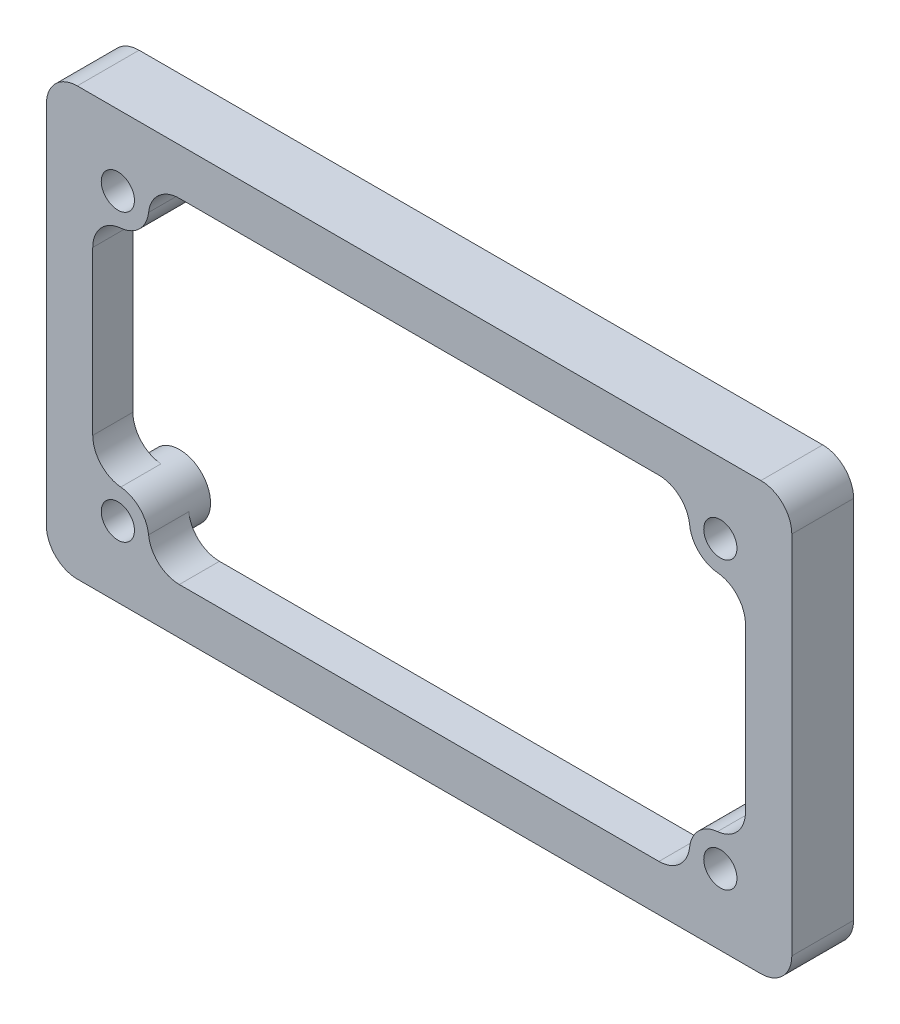
SolidWorks part; units mm, degrees
material "ABS"
ref_plane "Front Plane" through (0, 0, 0) normal (0, 0, 1) x (1, 0, 0)
ref_plane "Top Plane" through (0, 0, 0) normal (0, 1, 0) x (1, 0, 0)
ref_plane "Right Plane" through (0, 0, 0) normal (1, 0, 0) x (0, 0, -1)
sketch "Sketch1" plane through (0, 0, 0) normal (0, 0, 1) x (1, 0, 0)
  line L0 (-1.5, 26.15) -> (46.75, 26.15)
  line L1 (0, 0) -> (45.25, 0)
  line L2 (0, 0) -> (0, 24.65)
  line L3 (0, 24.65) -> (45.25, 24.65)
  line L4 (45.25, 0) -> (45.25, 24.65)
  line L5 (46.75, -1.5) -> (46.75, 26.15)
  line L6 (-1.5, -1.5) -> (46.75, -1.5)
  line L7 (-1.5, -1.5) -> (-1.5, 26.15)
  dimension "D1" = 24.65
  dimension "D2" = 45.25
  dimension "D3" = 1.5
extrude "Main Body" add sketch "Sketch1" along normal blind 4
sketch "Sketch3" plane through (0, 0, 4) normal (0, 0, 1) x (1, 0, 0)
  line L0 (0, 24.65) -> (0, 0)
  line L1 (0, 0) -> (45.25, 0)
  line L2 (45.25, 0) -> (45.25, 24.65)
  line L3 (45.25, 24.65) -> (0, 24.65)
  line L4 (1.5, 23.15) -> (1.5, 1.5)
  line L5 (1.5, 1.5) -> (43.75, 1.5)
  line L6 (43.75, 1.5) -> (43.75, 23.15)
  line L7 (43.75, 23.15) -> (1.5, 23.15)
  dimension "D1" = 1.5
extrude "Boss-Extrude2" add sketch "Sketch3" against normal offset from surface (2.6 mm away) 1.4 up to face at (22.625, 12.325, 0)
sketch "Sketch4" plane through (0, 0, 1.4) normal (0, 0, -1) x (-1, 0, 0)
  line L0 (0, 12.325) -> (-45.25, 12.325) construction
  line L1 (0, 24.65) -> (0, 0) construction
  line L2 (-45.25, 0) -> (-45.25, 24.65) construction
  line L3 (-22.625, 12.325) -> (-22.625, 24.65) construction
  line L4 (-45.25, 24.65) -> (0, 24.65) construction
  line L5 (-1.125, 21.575) -> (-1.125, 23.575)
  line L6 (-1.125, 23.575) -> (-3.125, 23.575)
  line L7 (-1.125, 1.075) -> (-3.125, 1.075)
  line L8 (-1.125, 3.075) -> (-1.125, 1.075)
  line L9 (-44.125, 3.075) -> (-44.125, 1.075)
  line L10 (-44.125, 1.075) -> (-42.125, 1.075)
  line L11 (-44.125, 23.575) -> (-42.125, 23.575)
  line L12 (-44.125, 21.575) -> (-44.125, 23.575)
  arc A0 (-3.125, 23.575) -> (-1.125, 21.575) centre (-3.125, 21.575) ccw
  arc A1 (-3.125, 1.075) -> (-1.125, 3.075) centre (-3.125, 3.075) cw
  arc A2 (-42.125, 1.075) -> (-44.125, 3.075) centre (-42.125, 3.075) ccw
  arc A3 (-42.125, 23.575) -> (-44.125, 21.575) centre (-42.125, 21.575) cw
  dimension "D1" = 4
  dimension "D2" = 39
  dimension "D3" = 18.5
extrude "Boss-Extrude3" add sketch "Sketch4" along normal up to surface and the other way up to surface
sketch "Sketch5" plane through (0, 0, 0) normal (0, 0, -1) x (-1, 0, 0)
  line L0 (-1.125, 23.575) -> (-1.125, 21.575) construction
  line L1 (-1.125, 23.575) -> (-3.125, 23.575) construction
  line L2 (-1.125, 23.575) -> (-1.125, 21.575)
  line L3 (-1.125, 23.575) -> (-3.125, 23.575)
  line L4 (-1.125, 1.075) -> (-1.125, 3.075) construction
  line L5 (-3.125, 1.075) -> (-1.125, 1.075) construction
  line L6 (-44.125, 1.075) -> (-42.125, 1.075) construction
  line L7 (-44.125, 3.075) -> (-44.125, 1.075) construction
  line L8 (-42.125, 23.575) -> (-44.125, 23.575) construction
  line L9 (-44.125, 23.575) -> (-44.125, 21.575) construction
  line L10 (-1.125, 1.075) -> (-1.125, 3.075)
  line L11 (-3.125, 1.075) -> (-1.125, 1.075)
  line L12 (-44.125, 1.075) -> (-42.125, 1.075)
  line L13 (-44.125, 3.075) -> (-44.125, 1.075)
  line L14 (-42.125, 23.575) -> (-44.125, 23.575)
  line L15 (-44.125, 23.575) -> (-44.125, 21.575)
  circle A0 centre (-3.125, 21.575) radius 1.075
  circle A1 centre (-3.125, 3.075) radius 1.075
  circle A2 centre (-42.125, 21.575) radius 1.075
  circle A3 centre (-42.125, 3.075) radius 1.075
  arc A4 (-42.125, 23.575) -> (-44.125, 21.575) centre (-42.125, 21.575) ccw
  arc A5 (-44.125, 3.075) -> (-42.125, 1.075) centre (-42.125, 3.075) ccw
  arc A6 (-1.125, 21.575) -> (-3.125, 23.575) centre (-3.125, 21.575) ccw
  arc A7 (-1.125, 3.075) -> (-3.125, 1.075) centre (-3.125, 3.075) cw
  arc A8 (-1.125, 3.075) -> (-3.125, 1.075) centre (-3.125, 3.075) ccw construction
  line M1 (-1.125, 23.575) -> (-3.125, 23.575)
  line M3 (-1.125, 21.575) -> (-1.125, 23.575)
  dimension "D1" = 2.15
extrude "Cut-Extrude1" cut sketch "Sketch5" against normal up to surface (1.4 mm away) contours A6 M3 M1 | A0 | A1 | L10 A7 L11 | A3 | A5 L13 L12 | A2 | A4 L14 L15 up to face at (22.625, 12.325, 1.4)
sketch "Sketch6" plane through (0, 0, 1.4) normal (0, 0, -1) x (-1, 0, 0)
  circle A0 centre (-3.125, 21.575) radius 1.075 construction
  circle A1 centre (-3.125, 3.075) radius 1.075 construction
  circle A2 centre (-42.125, 3.075) radius 1.075 construction
  circle A3 centre (-42.125, 21.575) radius 1.075 construction
  circle A4 centre (-3.125, 21.575) radius 1.075
  circle A5 centre (-3.125, 3.075) radius 1.075
  circle A6 centre (-42.125, 3.075) radius 1.075
  circle A7 centre (-42.125, 21.575) radius 1.075
extrude "Cut-Extrude2" cut sketch "Sketch6" against normal through all
fillet "Fillet1" radius 2 16 edges at (43.75, 4.2409, 2.7) (40.8924, 1.5, 2.7) (40.8924, 23.15, 2.7) (43.75, 20.4091, 2.7) (4.3576, 1.5, 2.7) (1.5, 4.2409, 2.7) (1.5, 20.4091, 2.7) (4.3576, 23.15, 2.7) (45.25, 0, 0.7) (46.75, -1.5, 2) (45.25, 24.65, 0.7) (46.75, 26.15, 2) (0, 0, 0.7) (-1.5, -1.5, 2) (-1.5, 26.15, 2) (0, 24.65, 0.7)
ref_point "Point1"
